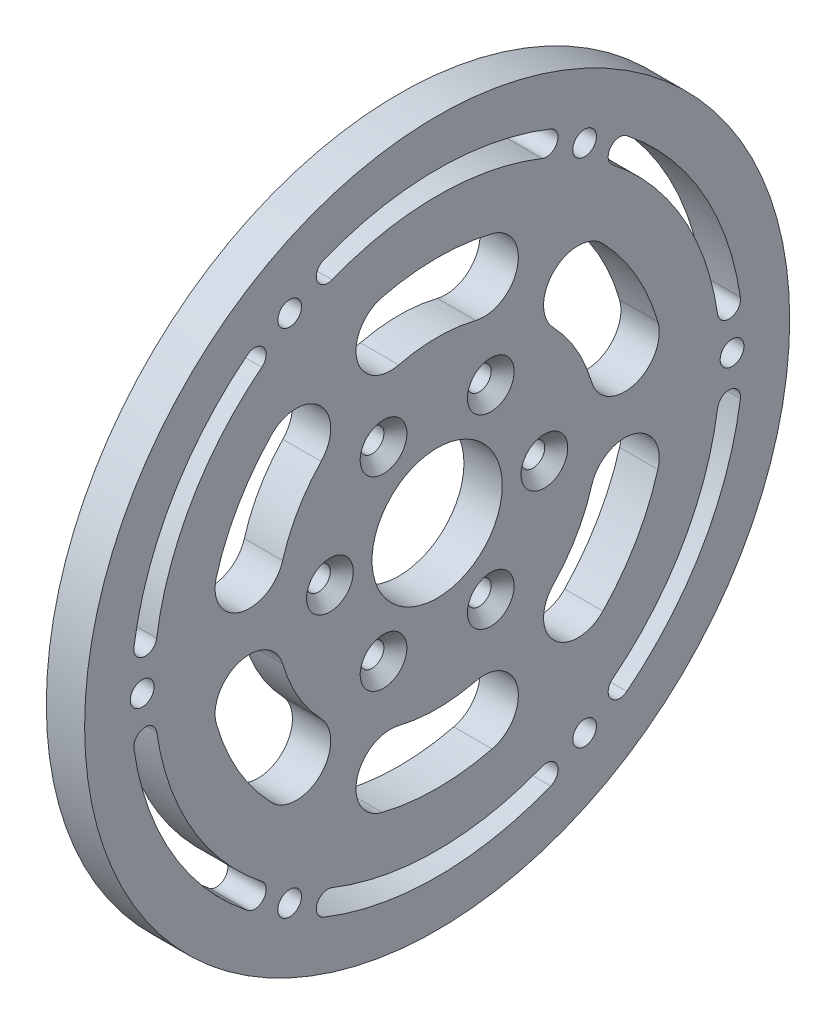
SolidWorks part; units mm, degrees
ref_plane "前视基准面" through (0, 0, 0) normal (0, 0, 1) x (1, 0, 0)
ref_plane "上视基准面" through (0, 0, 0) normal (0, 1, 0) x (1, 0, 0)
ref_plane "右视基准面" through (0, 0, 0) normal (1, 0, 0) x (0, 0, -1)
sketch "草图1" plane through (0, 0, 0) normal (0, 0, 1) x (1, 0, 0)
  line L0 (-2.5, 46.025) -> (-2.5, 0)
  line L1 (-2.5, 0) -> (2.5, 0)
  line L2 (2.5, 0) -> (2.5, 46.025)
  line L3 (2.5, 46.025) -> (-2.5, 46.025)
  line L4 (-2.5, 0) -> (2.5, 0) construction
revolve "旋转1" add sketch "草图1" angle 360 about L4
sketch "草图2" plane through (2.5, 0, 0) normal (1, 0, 0) x (0, 0, -1)
  arc A0 (20.1698, -5.8462) -> (15.1479, -14.5445) centre (0, 0) cw
  arc A1 (15.1479, -14.5445) -> (21.6398, -20.7778) centre (18.3939, -17.6611) ccw
  arc A2 (21.6398, -20.7778) -> (28.814, -8.3518) centre (0, 0) ccw
  arc A3 (28.814, -8.3518) -> (20.1698, -5.8462) centre (24.4919, -7.099) ccw
extrude "切除-拉伸1" cut sketch "草图2" against normal through all
sketch "草图3" plane through (2.5, 0, 0) normal (1, 0, 0) x (0, 0, -1)
  arc A0 (5.0219, -20.3907) -> (-5.0219, -20.3907) centre (0, 0) cw
  arc A1 (-5.0219, -20.3907) -> (-7.1742, -29.1296) centre (-6.0981, -24.7601) ccw
  arc A2 (-7.1742, -29.1296) -> (7.1742, -29.1296) centre (0, 0) ccw
  arc A3 (7.1742, -29.1296) -> (5.0219, -20.3907) centre (6.0981, -24.7601) ccw
extrude "切除-拉伸2" cut sketch "草图3" against normal through all
sketch "草图4" plane through (2.5, 0, 0) normal (1, 0, 0) x (0, 0, -1)
  arc A0 (-15.1479, -14.5445) -> (-20.1698, -5.8462) centre (0, 0) cw
  arc A1 (-20.1698, -5.8462) -> (-28.814, -8.3518) centre (-24.4919, -7.099) ccw
  arc A2 (-28.814, -8.3518) -> (-21.6398, -20.7778) centre (0, 0) ccw
  arc A3 (-21.6398, -20.7778) -> (-15.1479, -14.5445) centre (-18.3939, -17.6611) ccw
extrude "切除-拉伸3" cut sketch "草图4" against normal through all
sketch "草图5" plane through (2.5, 0, 0) normal (1, 0, 0) x (0, 0, -1)
  arc A0 (15.1479, 14.5445) -> (20.1698, 5.8462) centre (0, 0) cw
  arc A1 (20.1698, 5.8462) -> (28.814, 8.3518) centre (24.4919, 7.099) ccw
  arc A2 (28.814, 8.3518) -> (21.6398, 20.7778) centre (0, 0) ccw
  arc A3 (21.6398, 20.7778) -> (15.1479, 14.5445) centre (18.3939, 17.6611) ccw
extrude "切除-拉伸4" cut sketch "草图5" against normal through all
sketch "草图6" plane through (2.5, 0, 0) normal (1, 0, 0) x (0, 0, -1)
  arc A0 (-20.1698, 5.8462) -> (-15.1479, 14.5445) centre (0, 0) cw
  arc A1 (-15.1479, 14.5445) -> (-21.6398, 20.7778) centre (-18.3939, 17.6611) ccw
  arc A2 (-21.6398, 20.7778) -> (-28.814, 8.3518) centre (0, 0) ccw
  arc A3 (-28.814, 8.3518) -> (-20.1698, 5.8462) centre (-24.4919, 7.099) ccw
extrude "切除-拉伸5" cut sketch "草图6" against normal through all
sketch "草图7" plane through (2.5, 0, 0) normal (1, 0, 0) x (0, 0, -1)
  arc A0 (5.0219, 20.3907) -> (7.1742, 29.1296) centre (6.0981, 24.7601) ccw
  arc A1 (7.1742, 29.1296) -> (-7.1742, 29.1296) centre (0, 0) ccw
  arc A2 (-7.1742, 29.1296) -> (-5.0219, 20.3907) centre (-6.0981, 24.7601) ccw
  arc A3 (-5.0219, 20.3907) -> (5.0219, 20.3907) centre (0, 0) cw
extrude "切除-拉伸6" cut sketch "草图7" against normal through all
sketch "草图8" plane through (2.5, 0, 0) normal (1, 0, 0) x (0, 0, -1)
  arc A0 (-22.8978, 29.0636) -> (-24.7544, 31.4201) centre (-23.8261, 30.2418) ccw
  arc A1 (-24.7544, 31.4201) -> (-39.5878, 5.7279) centre (0, 0) ccw
  arc A2 (-39.5878, 5.7279) -> (-36.6187, 5.2983) centre (-38.1032, 5.5131) ccw
  arc A3 (-36.6187, 5.2983) -> (-22.8978, 29.0636) centre (0, 0) cw
extrude "切除-拉伸7" cut sketch "草图8" against normal through all
sketch "草图9" plane through (2.5, 0, 0) normal (1, 0, 0) x (0, 0, -1)
  arc A0 (-36.6187, -5.2983) -> (-39.5878, -5.7279) centre (-38.1032, -5.5131) ccw
  arc A1 (-39.5878, -5.7279) -> (-24.7544, -31.4201) centre (0, 0) ccw
  arc A2 (-24.7544, -31.4201) -> (-22.8978, -29.0636) centre (-23.8261, -30.2418) ccw
  arc A3 (-22.8978, -29.0636) -> (-36.6187, -5.2983) centre (0, 0) cw
extrude "切除-拉伸8" cut sketch "草图9" against normal through all
sketch "草图10" plane through (2.5, 0, 0) normal (1, 0, 0) x (0, 0, -1)
  arc A0 (-13.7209, -34.3619) -> (-14.8334, -37.1479) centre (-14.2772, -35.7549) ccw
  arc A1 (-14.8334, -37.1479) -> (14.8334, -37.1479) centre (0, 0) ccw
  arc A2 (14.8334, -37.1479) -> (13.7209, -34.3619) centre (14.2772, -35.7549) ccw
  arc A3 (13.7209, -34.3619) -> (-13.7209, -34.3619) centre (0, 0) cw
extrude "切除-拉伸9" cut sketch "草图10" against normal through all
sketch "草图11" plane through (2.5, 0, 0) normal (1, 0, 0) x (0, 0, -1)
  arc A0 (13.7209, 34.3619) -> (14.8334, 37.1479) centre (14.2772, 35.7549) ccw
  arc A1 (14.8334, 37.1479) -> (-14.8334, 37.1479) centre (0, 0) ccw
  arc A2 (-14.8334, 37.1479) -> (-13.7209, 34.3619) centre (-14.2772, 35.7549) ccw
  arc A3 (-13.7209, 34.3619) -> (13.7209, 34.3619) centre (0, 0) cw
extrude "切除-拉伸10" cut sketch "草图11" against normal through all
sketch "草图12" plane through (2.5, 0, 0) normal (1, 0, 0) x (0, 0, -1)
  arc A0 (22.8978, -29.0636) -> (24.7544, -31.4201) centre (23.8261, -30.2418) ccw
  arc A1 (24.7544, -31.4201) -> (39.5878, -5.7279) centre (0, 0) ccw
  arc A2 (39.5878, -5.7279) -> (36.6187, -5.2983) centre (38.1032, -5.5131) ccw
  arc A3 (36.6187, -5.2983) -> (22.8978, -29.0636) centre (0, 0) cw
extrude "切除-拉伸11" cut sketch "草图12" against normal through all
sketch "草图13" plane through (-2.5, 0, 0) normal (-1, 0, 0) x (0, 0, 1)
  arc A0 (-39.5878, 5.7279) -> (-36.6187, 5.2983) centre (-38.1032, 5.5131) ccw
  arc A1 (-36.6187, 5.2983) -> (-22.8978, 29.0636) centre (0, 0) cw
  arc A2 (-22.8978, 29.0636) -> (-24.7544, 31.4201) centre (-23.8261, 30.2418) ccw
  arc A3 (-24.7544, 31.4201) -> (-39.5878, 5.7279) centre (0, 0) ccw
extrude "切除-拉伸12" cut sketch "草图13" against normal through all
hole_wizard "Ø17.0 (17) 直径孔1" positions "草图15" profile "草图14" hole size "Ø17.0" standard "ANSI Metric"
sketch "草图15" plane through (2.5, 0, 0) normal (1, 0, 0) x (0, 0, -1)
  point P0 (0, 0)
sketch "草图14" plane through (2.5, 0, 0) normal (0, 1, 0) x (0, 0, -1)
  line L0 (0, 0) -> (0, 5)
  line L1 (0, 5) -> (8.5, 5)
  line L2 (8.5, 5) -> (8.5, 0)
  line L5 (8.5, 0) -> (0, 0)
  line L11 (0, -6.35) -> (0, 107.95) construction
  dimension "通孔孔直径" = 17
  dimension "通孔孔深度" = 5
hole_wizard "Ø3.0 (3) 直径孔1" positions "草图17" profile "草图16" hole size "Ø3.0" standard "ANSI Metric"
sketch "草图17" plane through (2.5, 0, 0) normal (1, 0, 0) x (0, 0, -1)
  point P0 (-14, 0)
  point P1 (-7, 12.1244)
  point P2 (7, 12.1244)
  point P3 (14, 0)
  point P4 (7, -12.1244)
  point P5 (-7, -12.1244)
  point P6 (19.25, -33.342)
  point P7 (19.25, 33.342)
  point P8 (-38.5, 0)
  point P9 (38.5, 0)
  point P10 (-19.25, -33.342)
  point P11 (-19.25, 33.342)
sketch "草图16" plane through (2.5, 0, 14) normal (0, 1, 0) x (0, 0, -1)
  line L0 (0, 0) -> (0, 5)
  line L1 (0, 5) -> (1.55, 5)
  line L2 (1.55, 5) -> (1.55, 0)
  line L5 (1.55, 0) -> (0, 0)
  line L11 (0, -6.35) -> (0, 107.95) construction
  dimension "通孔孔直径" = 3.1
  dimension "通孔孔深度" = 5
chamfer "倒角1" distance 1.5 angle 45 6 edges at (2.5, 0, -15.55) (2.5, -12.1244, 5.45) (2.5, -12.1244, -8.55) (2.5, 12.1244, 5.45) (2.5, 0, 12.45) (2.5, 12.1244, -8.55)
